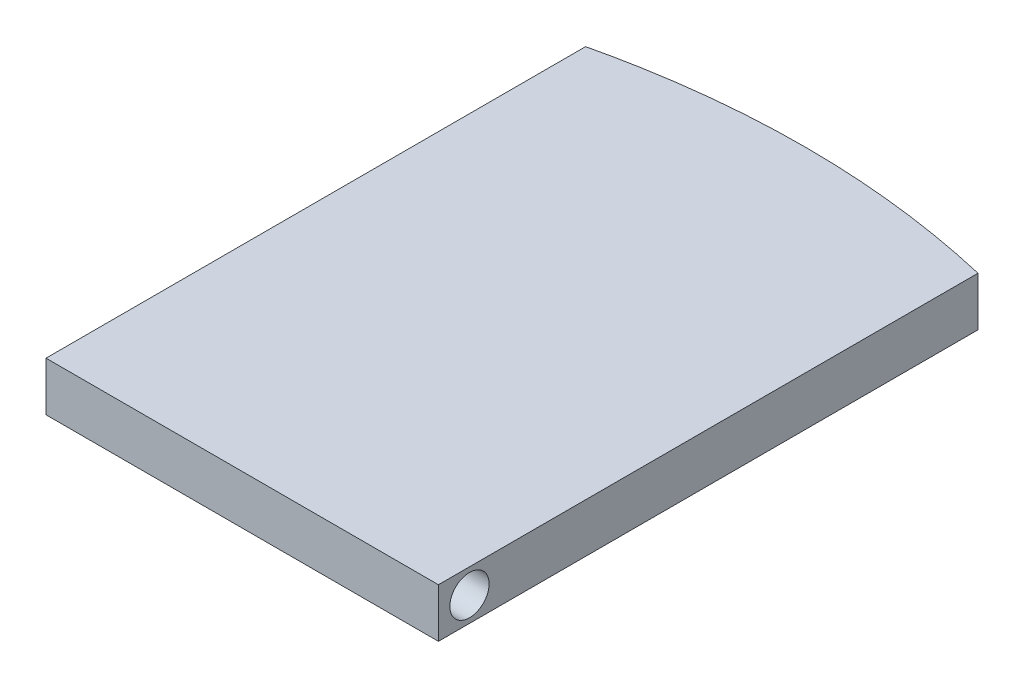
SolidWorks part; units mm, degrees
ref_plane "Front Plane" through (0, 0, 0) normal (0, 0, 1) x (1, 0, 0)
ref_plane "Top Plane" through (0, 0, 0) normal (0, 1, 0) x (1, 0, 0)
ref_plane "Right Plane" through (0, 0, 0) normal (1, 0, 0) x (0, 0, -1)
sketch "Sketch1" plane through (0, 0, 0) normal (0, 1, 0) x (1, 0, 0)
  line L0 (0, 0) -> (24, 0)
  line L1 (12, 0) -> (12, 35) construction
  line L2 (0, 0) -> (0, 33.6) construction
  line L3 (24, 0) -> (24, 33.6) construction
  line L4 (0, 0) -> (0, 33.6)
  line L5 (24, 0) -> (24, 33.6)
  spline S0 degree 2 poles (0, 33.6) (12, 36.4) (24, 33.6) knots 0 0 0 1 1 1
  dimension "D1" = 24
  dimension "D2" = 33.6
extrude "Boss-Extrude1" add sketch "Sketch1" along normal blind 3
sketch "Sketch2" plane through (24, 0, 0) normal (1, 0, 0) x (0, 0, -1)
  line L0 (0, 1.5) -> (33.6, 1.5) construction
  line L1 (0, 3) -> (0, 0) construction
  line L2 (33.6, 3) -> (33.6, 0) construction
  line L3 (2.5, 3) -> (2.5, 0) construction
  line L4 (0, 3) -> (33.6, 3) construction
  line L5 (0, 0) -> (33.6, 0) construction
  circle A0 centre (2.5, 1.5) radius 1.2
  dimension "D2" = 2.4
  dimension "D1" = 2.5
extrude "Cut-Extrude1" cut sketch "Sketch2" against normal blind 7
sketch "Sketch3" plane through (0, 0, 0) normal (-1, 0, 0) x (0, 0, 1)
  line L0 (-33.6, 1.5) -> (0, 1.5) construction
  line L1 (-33.6, 3) -> (-33.6, 0) construction
  line L2 (0, 3) -> (0, 0) construction
  line L3 (-2.5, 0) -> (-2.5, 3) construction
  line L4 (-33.6, 0) -> (0, 0) construction
  line L5 (-33.6, 3) -> (0, 3) construction
  circle A0 centre (-2.5, 1.5) radius 1.2
  dimension "D2" = 2.4
  dimension "D1" = 2.5
extrude "Cut-Extrude2" cut sketch "Sketch3" against normal blind 7
sketch "Sketch4" plane through (0, 3, 0) normal (0, 1, 0) x (1, 0, 0)
  line L0 (24, 0) -> (24, 33.6) construction
  line L1 (0, 0) -> (24, 0)
  line L2 (0, 0) -> (0, 0.6)
  line L3 (0, 0.6) -> (24, 0.6)
  line L4 (24, 0) -> (24, 0.6)
  dimension "D1" = 0.6
extrude "Cut-Extrude3" cut sketch "Sketch4" against normal through all
